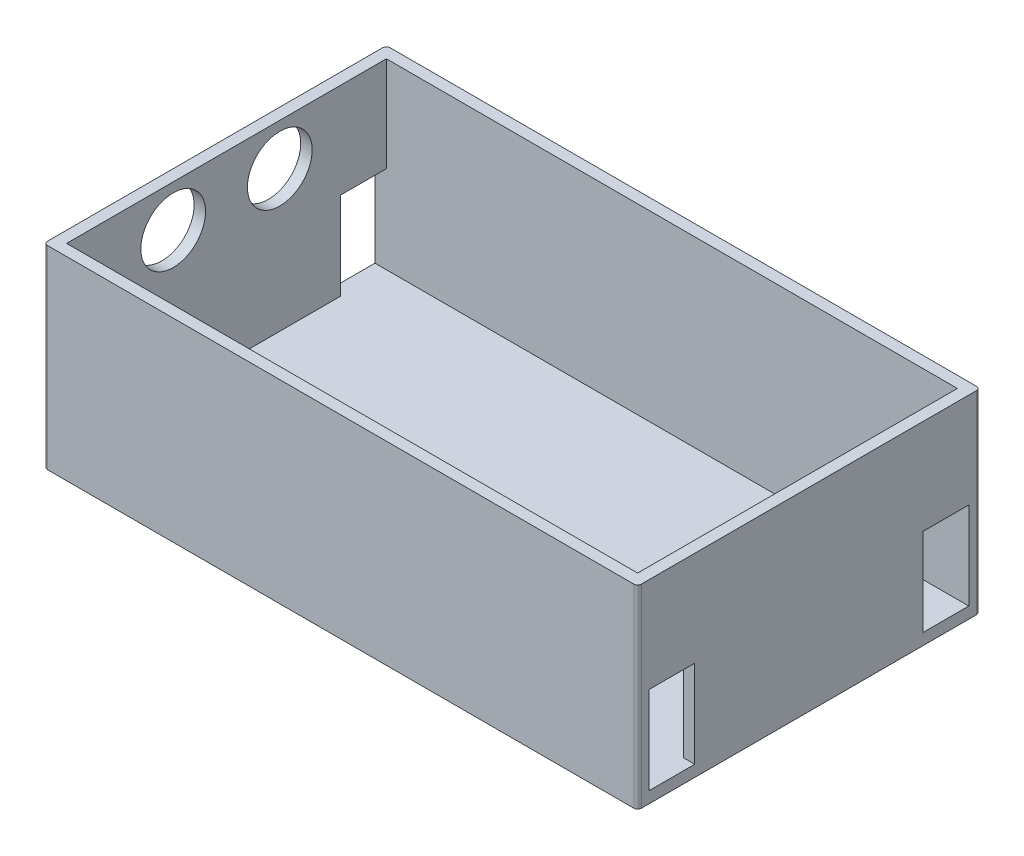
SolidWorks part; units mm, degrees
ref_plane "Front Plane" through (0, 0, 0) normal (0, 0, 1) x (1, 0, 0)
ref_plane "Top Plane" through (0, 0, 0) normal (0, 1, 0) x (1, 0, 0)
ref_plane "Right Plane" through (0, 0, 0) normal (1, 0, 0) x (0, 0, -1)
sketch "Sketch1" plane through (0, 0, 0) normal (0, 1, 0) x (1, 0, 0)
  line L1 (0, 0) -> (156, 0)
  line L2 (0, 0) -> (0, 90)
  line L3 (0, 90) -> (156, 90)
  line L4 (156, 0) -> (156, 90)
  dimension "D1" = 90
  dimension "D2" = 156
extrude "Boss-Extrude1" add sketch "Sketch1" along normal blind 3
sketch "Sketch2" plane through (0, 3, 0) normal (0, 1, 0) x (1, 0, 0)
  line L1 (3, 87) -> (153, 87)
  line L2 (3, 87) -> (3, 3)
  line L3 (3, 3) -> (153, 3)
  line L4 (0, 90) -> (0, 0)
  line L5 (0, 0) -> (156, 0)
  line L6 (156, 0) -> (156, 90)
  line L7 (156, 90) -> (0, 90)
  line L8 (0, 90) -> (0, 0)
  line L9 (0, 0) -> (156, 0)
  line L10 (156, 0) -> (156, 90)
  line L11 (156, 90) -> (0, 90)
  line L12 (153, 87) -> (153, 3)
  dimension "D2" = 3
  dimension "D3" = 3
  dimension "D4" = 3
  dimension "D5" = 3
  dimension "D1" = 0
extrude "Boss-Extrude2" add sketch "Sketch2" along normal blind 48
fillet "Fillet1" radius 1 4 edges at (156, 25.5, -90) (0, 25.5, -90) (156, 25.5, 0) (0, 25.5, 0)
sketch "Sketch3" plane through (156, 0, 0) normal (1, 0, 0) x (0, 0, -1)
  line L0 (0, 0) -> (0, 51) construction
  line L1 (3, 26) -> (15, 26)
  line L2 (3, 26) -> (3, 3)
  line L3 (3, 3) -> (15, 3)
  line L4 (15, 26) -> (15, 3)
  line L5 (1, 0) -> (89, 0) construction
  line L6 (90, 51) -> (90, 0) construction
  line L7 (87, 3) -> (75, 3)
  line L8 (87, 3) -> (87, 26)
  line L9 (87, 26) -> (75, 26)
  line L10 (75, 3) -> (75, 26)
  dimension "D1" = 3
  dimension "D2" = 3
  dimension "D3" = 12
  dimension "D4" = 23
  dimension "D5" = 3
  dimension "D6" = 3
extrude "Cut-Extrude2" cut sketch "Sketch3" against normal through all
sketch "Sketch4" plane through (0, 0, 0) normal (-1, 0, 0) x (0, 0, 1)
  line L0 (-89, 51) -> (-1, 51) construction
  line L1 (-90, 0) -> (-90, 51) construction
  circle A0 centre (-59, 40) radius 8.5
  circle A1 centre (-31, 40) radius 8.5
  point P4 (0, 0)
  point P7 (0, 0)
  point P8 (0, 0)
  dimension "D2" = 17
  dimension "D4" = 31
  dimension "D1" = 11
  dimension "D3" = 28
extrude "Cut-Extrude3" cut sketch "Sketch4" against normal blind 10
